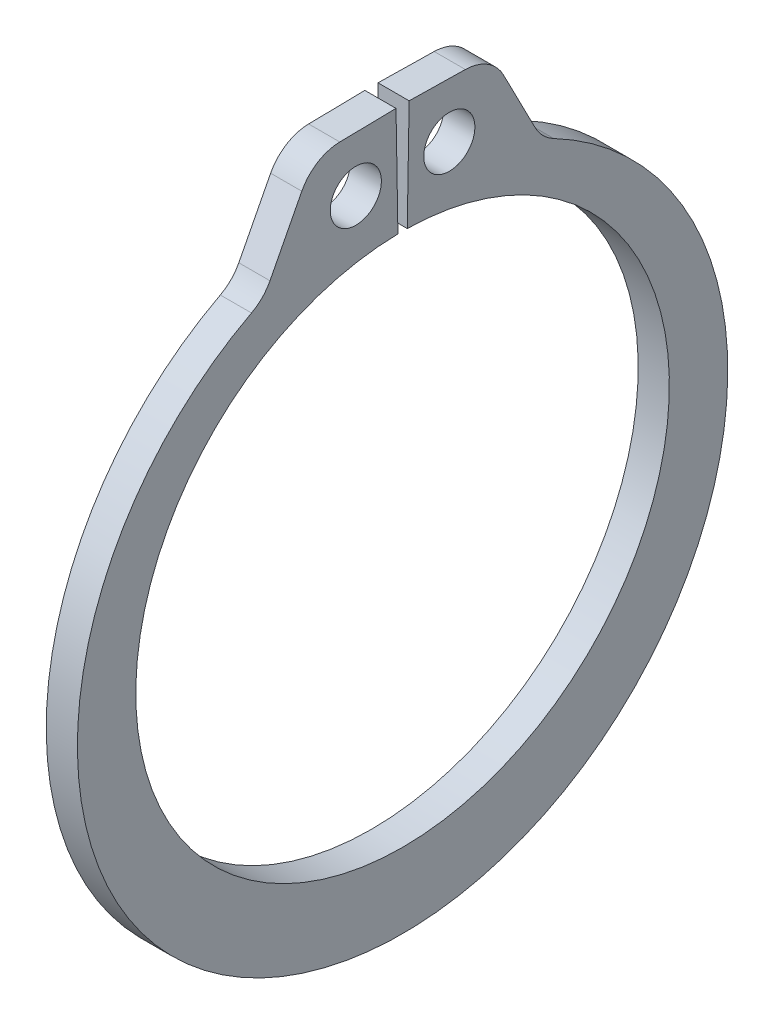
SolidWorks part; units mm, degrees
material "Cast Carbon Steel"
ref_plane "Front" through (0, 0, 0) normal (0, 0, 1) x (1, 0, 0)
ref_plane "Top" through (0, 0, 0) normal (0, 1, 0) x (1, 0, 0)
ref_plane "Right" through (0, 0, 0) normal (1, 0, 0) x (0, 0, -1)
sketch "Sketch1" plane through (0, 0, 0) normal (1, 0, 0) x (0, 0, -1)
  line L0 (0, 0) -> (0, 5.4356) construction
  line L1 (-0.0949, 5.4348) -> (-0.1339, 7.6696)
  line L2 (0.1339, 7.6696) -> (1.81, 7.6404)
  line L3 (1.81, 7.6404) -> (2.8346, 5.6538)
  line L4 (0.0949, 5.4348) -> (0.1339, 7.6696)
  line L5 (-0.1339, 7.6696) -> (-1.81, 7.6404)
  line L6 (-1.81, 7.6404) -> (-2.8346, 5.6538)
  line L7 (-2.8346, 5.6538) -> (-2.4361, 4.8591) construction
  line L8 (2.8346, 5.6538) -> (2.4361, 4.8591) construction
  line L9 (0, -5.4356) -> (0, -6.9596) construction
  line L10 (-1.81, 7.6404) -> (-0.0949, 5.4348) construction
  line L11 (0, 5.4356) -> (0, 7.6708) construction
  line L12 (-5.4356, 0) -> (5.4356, 0) construction
  circle A0 centre (0, 0) radius 5.4356 construction
  arc A1 (-0.0949, 5.4348) -> (0.0949, 5.4348) centre (0, 0) ccw
  circle A3 centre (0, 0) radius 8.509 construction
  circle A4 centre (-0.9524, 6.5376) radius 0.5207
  circle A5 centre (0.9524, 6.5376) radius 0.5207
  arc A6 (-2.8346, 5.6538) -> (2.8346, 5.6538) centre (0, -0.3344) ccw
  point P0 (0, -6.9596)
  dimension "A" = 10.8712
  dimension "D2" = 1.6764
  dimension "L" = 17.018
  dimension "Hole" = 1.0414
  dimension "Smin" = 0.889
  dimension "Smax" = 1.524
  dimension "H" = 2.2352
  dimension "Angle" = 1
extrude "Extrude1" add sketch "Sketch1" along normal mid plane 0.635
fillet "Fillet1" radius 0.889 4 edges at (0, 5.6538, 2.8346) (0, 5.6538, -2.8346) (0, 7.6404, 1.81) (0, 7.6404, -1.81)
sketch "Sketch2" plane through (0, 0, 0) normal (0, 0, 1) x (1, 0, 0)
  line L0 (-3.5433, 0) -> (9.1567, 0)
  line L1 (9.1567, 0) -> (9.1567, -5.9563)
  line L2 (-0.3683, -5.9563) -> (-3.2131, -5.9563)
  line L3 (9.1567, -5.9563) -> (0.3683, -5.9563)
  line L4 (0.3683, -5.9563) -> (0.3683, -5.6261)
  line L5 (0.3683, -5.6261) -> (-0.3683, -5.6261)
  line L6 (-0.3683, -5.6261) -> (-0.3683, -5.9563)
  line L7 (-0.3683, -5.9563) -> (-3.5433, -5.9563) construction
  line L8 (-3.5433, -5.9563) -> (-3.5433, 0) construction
  line L9 (9.1567, 0) -> (76.391, 0) construction
  line L10 (-3.2131, -5.9563) -> (-3.5433, -5.6261)
  line L11 (-3.5433, -5.6261) -> (-3.5433, 0)
  point P10 (0, -5.6261)
  dimension "D1" = 45
  dimension "Dg" = 11.2522
  dimension "Ds" = 11.9126
  dimension "W" = 0.7366
  dimension "D2" = 12.7
  dimension "D3" = 3.175
revolve "Revolve1" [suppressed] add sketch "Sketch2" angle 360 about L9
delete or keep bodies "Body-Delete1" [suppressed] type delete bodies bodies 122
equation "\"D2@Sketch2\" = \"D1@Extrude1\"*20"
equation "\"D3@Sketch2\" = \"D2@Sketch2\"/4"
equation "\"D2@Sketch1\" = \"H@Sketch1\"*.75"
